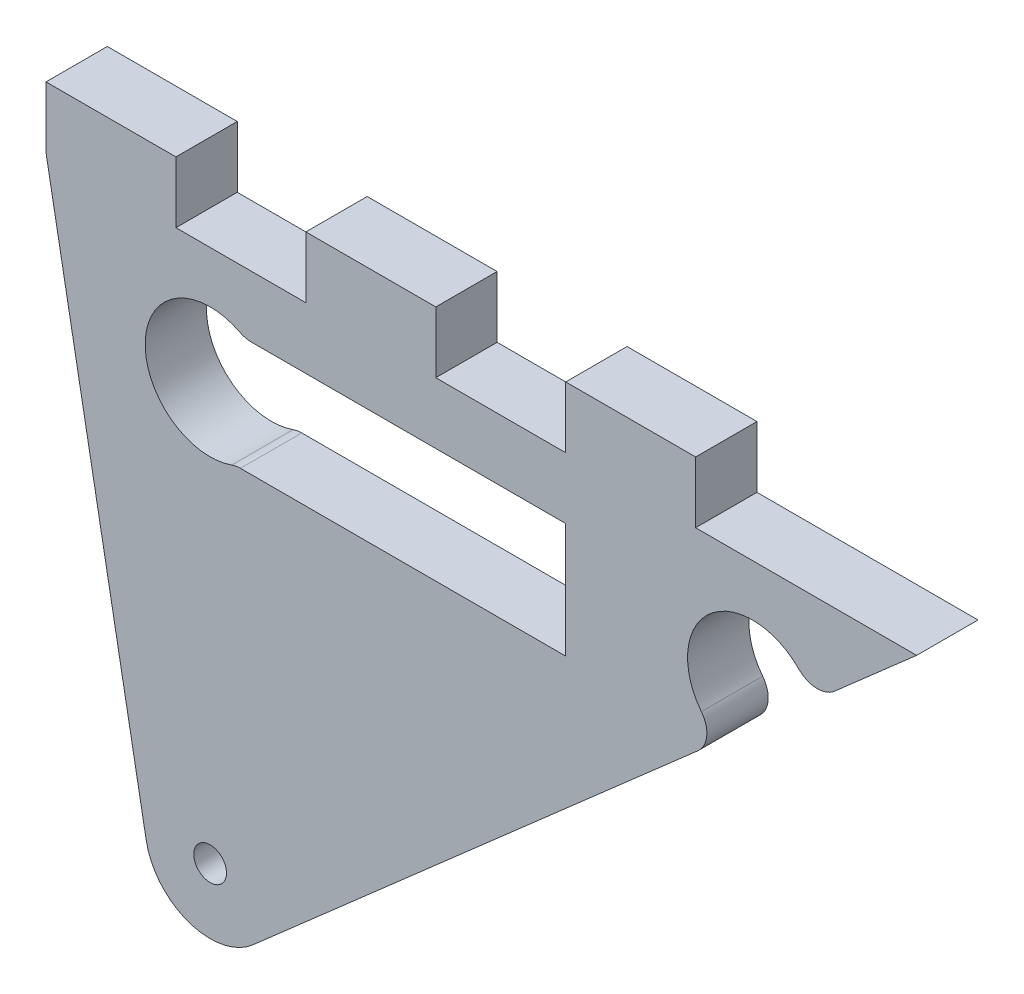
SolidWorks part; units mm, degrees
ref_plane "Front Plane" through (0, 0, 0) normal (0, 0, 1) x (1, 0, 0)
ref_plane "Top Plane" through (0, 0, 0) normal (0, 1, 0) x (1, 0, 0)
ref_plane "Right Plane" through (0, 0, 0) normal (1, 0, 0) x (0, 0, -1)
sketch "Sketch1" plane through (0, 0, 0) normal (0, 0, 1) x (1, 0, 0)
  line L0 (339.3467, 72.45) -> (337.0335, 72.45)
  line L1 (316.9956, 78.2168) -> (326.7498, 25.1342)
  line L2 (316.9538, 78.6758) -> (316.9538, 84.4388)
  line L3 (316.9538, 84.4388) -> (329.6538, 84.4388)
  line L4 (330.7726, 61.2277) -> (341.7726, 61.2277) construction
  line L5 (329.6538, 84.4388) -> (329.6538, 78.4444)
  line L6 (367.7538, 72.45) -> (339.3467, 72.45)
  line L7 (329.6538, 78.4444) -> (342.3538, 78.4444)
  line L8 (367.7538, 72.45) -> (367.7538, 61.2277)
  line L9 (342.3538, 78.4444) -> (342.3538, 84.4388)
  line L10 (342.3538, 84.4388) -> (355.0538, 84.4388)
  line L11 (355.0538, 84.4388) -> (355.0538, 78.4444)
  line L12 (402.0588, 78.4444) -> (394.0278, 71.3959)
  line L13 (355.0538, 78.4444) -> (367.7538, 78.4444)
  line L14 (367.7538, 78.4444) -> (367.7538, 84.4388)
  line L15 (367.7538, 84.4388) -> (380.4538, 84.4388)
  line L16 (380.4538, 84.4388) -> (380.4538, 78.4444)
  line L17 (367.7538, 61.2277) -> (339.3467, 61.2277)
  line L18 (380.4538, 78.4444) -> (402.0588, 78.4444)
  line L19 (402.0588, 78.4444) -> (401.9903, 78.5437)
  line L20 (380.6863, 59.6866) -> (337.1864, 21.5084)
  line L22 (339.3467, 61.2277) -> (335.9597, 61.2277)
  circle A0 centre (332.9967, 26.2821) radius 1.6
  arc A1 (326.7498, 25.1342) -> (337.1864, 21.5084) centre (332.9967, 26.2821) ccw
  arc A2 (335.8802, 72.727) -> (335.1131, 61.0825) centre (332.9967, 67.0694) ccw
  arc A3 (390.5419, 71.5234) -> (381.0123, 63.1596) centre (386.0159, 67.0694) ccw
  arc A4 (316.9956, 78.2168) -> (316.9538, 78.6758) centre (319.4938, 78.6758) cw
  arc A5 (390.5419, 71.5234) -> (394.0278, 71.3959) centre (392.3523, 73.3049) ccw
  arc A6 (381.0123, 63.1596) -> (380.6863, 59.6866) centre (379.0108, 61.5957) cw
  arc A7 (337.0335, 72.45) -> (335.8802, 72.727) centre (337.0335, 74.99) cw
  arc A8 (335.9597, 61.2277) -> (335.1131, 61.0825) centre (335.9597, 58.6877) ccw
  point P35 (316.9538, 78.4444)
  point P41 (382.8357, 61.5731)
  point P42 (335.4861, 61.2277)
  point P43 (428.8668, 88.5408)
  dimension "D1" = 2.54
  dimension "D2" = 2.54
  dimension "D3" = 2.54
  dimension "D4" = 12.7
  dimension "D5" = 2.54
  dimension "D6" = 2.54
extrude "Boss-Extrude1" add sketch "Sketch1" along normal blind 5.9944 contours A6 A3 A5 L12 L18 L16 L15 L14 L13 L11 L10 L9 L7 L5 L3 L2 A4 L1 A1 L20 A2 A0
